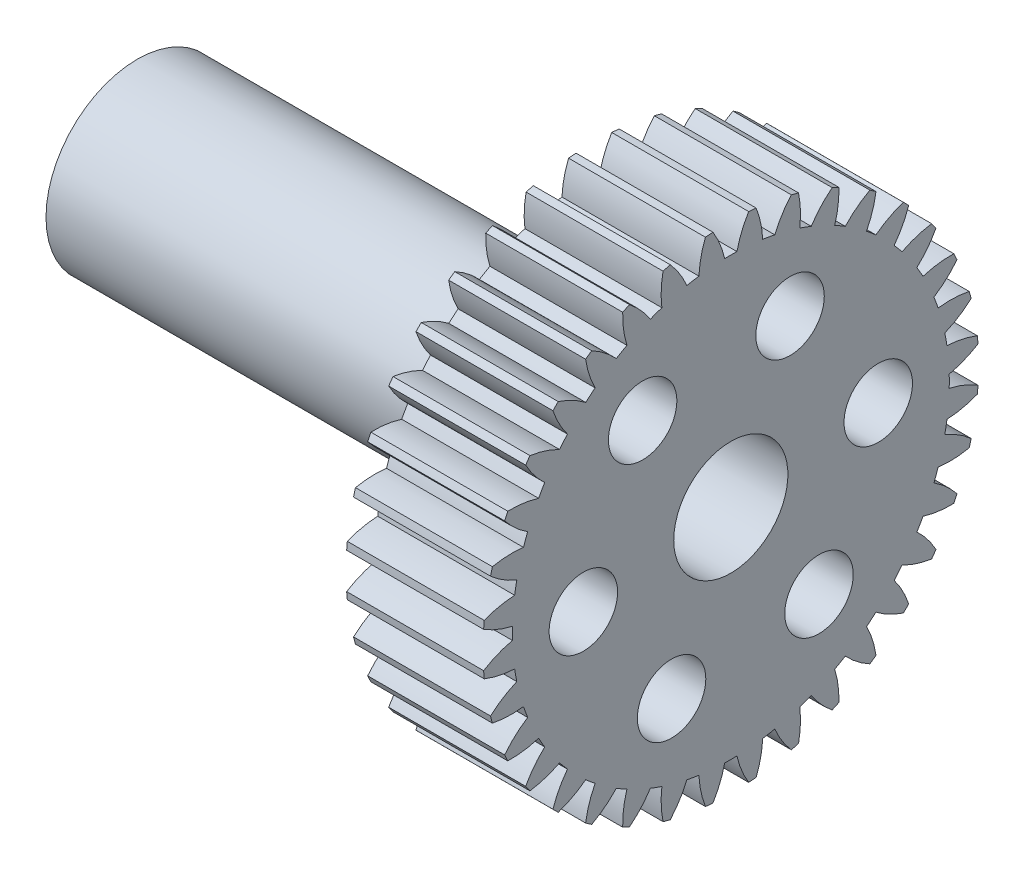
SolidWorks part; units mm, degrees
ref_plane "Plane1" through (0, 0, 0) normal (0, 0, 1) x (1, 0, 0)
ref_plane "Plane2" through (0, 0, 0) normal (0, 1, 0) x (1, 0, 0)
ref_plane "Plane3" through (0, 0, 0) normal (1, 0, 0) x (0, 0, -1)
sketch "HoldingSke" plane through (0, 0, 0) normal (0, 1, 0) x (1, 0, 0)
  line L0 (0, 0) -> (287.6864, -209.0164)
  line L1 (-15, 0) -> (100, 0) construction
  line L2 (0, 0) -> (-2.1039, 2.3779)
  line L3 (0, 0) -> (-11.863, 4.5341)
  line L4 (0, 0) -> (6.9867, 5.0761)
  line L5 (0, 0) -> (-77.3455, -28.8476)
  line L6 (0, 0) -> (-15.7917, -10.6547)
  line L7 (-2.1039, 2.3779) -> (15.665, 82.9929)
  line L8 (-76.2, 54.61) -> (-58.1914, 54.61)
  line L9 (-71.009, 38.7566) -> (-53.1078, 45.2721)
  line L10 (-76.2, 71.12) -> (104.1128, 71.12)
  line L11 (0, 0) -> (-19.05, 0)
  line L12 (-76.2, 101.6) -> (-76.1147, 101.6)
  line L13 (24.9733, 27.94) -> (52.9518, 28.4284)
  line L14 (24.9733, 27.94) -> (24.9746, 27.94)
  line L15 (24.9733, 27.94) -> (100.4006, 29.5858)
  circle A0 centre (0, 0) radius 7.9375
  circle A1 centre (0, 0) radius 12.7
  circle A2 centre (0, 0) radius 12.7
  circle A3 centre (0, 0) radius 7.9375
  dimension "MHD" = 25.4
  dimension "Hub_dia" = 25.4
  dimension "Bore" = 15.875
  dimension "MBD" = 15.875
  dimension "Num_teeth" = 36
  dimension "Pitch" = 355.6
  dimension "Overall_len" = 82.55
  dimension "Show_teeth" = 36
  dimension "Thickness" = 19.05
  dimension "OAL" = 82.5501
  dimension "T_dim" = 18.0086
  dimension "Ap" = 20
  dimension "H" = 19.05
  dimension "Pitch_radius" = 180.3128
  dimension "Width" = 19.05
  dimension "Backlash" = 0.0853
  dimension "Addendum_fac" = 1
  dimension "Dedendum_fac" = 1.25
  dimension "Clearance_fac" = 0.25
  dimension "Dedendum_add" = 0.0013
sketch "BasProSke" plane through (0, 0, 0) normal (0, 1, 0) x (1, 0, 0)
  line L0 (-10, 0) -> (60, 0) construction
  line L1 (0, 0) -> (0, 34.4714)
  line L2 (0, 0) -> (19.05, 0)
  line L3 (19.05, 0) -> (19.05, 34.4714)
  line L4 (19.05, 34.4714) -> (0, 34.4714)
  dimension "Thickness" = 19.05
  dimension "Diameter" = 68.9429
revolve "Base-Revolve" add sketch "BasProSke" angle 360 about L0
sketch "TooCutSke" plane through (0, 0, 0) normal (1, 0, 0) x (0, 0, -1)
  line L1 (0, 0) -> (0, 107) construction
  line L2 (0, 0) -> (-1.5738, 32.6192) construction
  line L3 (0, 0) -> (-5.6882, 65.0161) construction
  line L4 (-1.5738, 32.6192) -> (-2.8441, 32.5081) construction
  arc A0 (0.8517, 30.3761) -> (-0.8517, 30.3761) centre (0, 0) ccw
  arc A1 (2.5015, 34.406) -> (-2.5015, 34.406) centre (0, 0) ccw
  circle A2 centre (0, 0) radius 32.6571 construction
  circle A3 centre (0, 0) radius 30.6877 construction
  arc A4 (-0.8517, 30.3761) -> (-2.5015, 34.406) centre (-13.5966, 27.5112) ccw
  arc A5 (2.5015, 34.406) -> (0.8517, 30.3761) centre (13.5966, 27.5112) ccw
  dimension "Root_dia" = 60.776
  dimension "Overcut_dia" = 68.9937
  dimension "Pitch_dia" = 65.3143
  dimension "Base_dia" = 61.3754
  dimension "Flank_rad" = 13.0629
  dimension "Half_ang" = 5
  dimension "Half_CT" = 1.2751
extrude "ToothCut" cut sketch "TooCutSke" along normal through all
fillet "Breaks" [suppressed] radius 0.0363
fillet "RootFillets" [suppressed] radius 0.4548
pattern_circular "TeethCuts" count 36 over 360 about axis through (0, 0, 0) along (1, 0, 0) of "ToothCut", "RootFillets", "Breaks"
sketch "HubNeaOneSke" plane through (0, 0, 0) normal (-1, 0, 0) x (0, 0, 1)
  circle A0 centre (0, 0) radius 12.7
  dimension "Diameter" = 25.4
extrude "HubNearOne" add sketch "HubNeaOneSke" along normal blind 63.5001
sketch "HubNeaBotSke" plane through (0, 0, 0) normal (-1, 0, 0) x (0, 0, 1)
  circle A0 centre (0, 0) radius 12.7
  dimension "Diameter" = 25.4
extrude "HubNearBoth" [suppressed] add sketch "HubNeaBotSke" along normal blind 31.75
ref_plane "FarPln" through (19.05, 0, 0) normal (1, 0, 0) x (0, 0, -1)
sketch "HubFarSke" plane through (19.05, 0, 0) normal (1, 0, 0) x (0, 0, -1)
  circle A0 centre (0, 0) radius 12.7
  dimension "Diameter" = 25.4
extrude "HubFar" [suppressed] add sketch "HubFarSke" along normal blind 31.75
sketch "BorSke" plane through (0, 0, 0) normal (1, 0, 0) x (0, 0, -1)
  circle A0 centre (0, 0) radius 7.9375
  dimension "Diameter" = 15.875
extrude "Bore" cut sketch "BorSke" along normal mid plane 165.1001
sketch "KeySke" plane through (0, 0, 0) normal (1, 0, 0) x (0, 0, -1)
  line L0 (-2.3813, 0) -> (-2.3813, 10.0711)
  line L1 (-2.3813, 10.0711) -> (2.3813, 10.0711)
  line L2 (2.3813, 10.0711) -> (2.3813, 0)
  line L3 (0, 0) -> (0, 34) construction
  line L4 (-2.3813, 0) -> (2.3813, 0)
  dimension "Offset" = 10.0711
  dimension "Width" = 4.7625
extrude "Keyway" [suppressed] cut sketch "KeySke" along normal mid plane 165.1001
pattern_circular "Keyway2" [suppressed] count 2 every 90 about axis through (-10, 0, 0) along (1, 0, 0)
sketch "Sketch3" plane through (-63.5001, 0, 0) normal (-1, 0, 0) x (0, 0, 1)
  circle A0 centre (0, 0) radius 8.7376
  point P2 (0, 0)
  point P4 (-0.7441, 7.6589)
extrude "Cut-Extrude1" cut sketch "Sketch3" against normal blind 15.875
sketch "Sketch10" plane through (19.05, 0, 0) normal (1, 0, 0) x (0, 0, -1)
  circle A2 centre (-12.2654, 16.5972) radius 4.7625
extrude "Cut-Extrude3" cut sketch "Sketch10" against normal blind 19.05 contours A2
pattern_circular "CirPattern3" count 6 over 360 about axis through (0, 0, 0) along (1, 0, 0) of "Cut-Extrude3"
equation "' \"Pitch@HoldingSke\" = 4"
equation "' \"Num_teeth@HoldingSke\" = 12"
equation "' \"Ap@HoldingSke\" =  20"
equation "' \"Ap@HoldingSke\" = 20"
equation "' \"Width@HoldingSke\" = 0.5"
equation "' \"Hub_dia@HoldingSke\"= 1"
equation "' \"Hub_dia@HoldingSke\" = 1"
equation "' \"Overall_len@HoldingSke\" = 1.0"
equation "' \"Bore@HoldingSke\" = 0.75"
equation "' \"T_dim@HoldingSke\" = 0.85"
equation "' \"Width@KeySke\" = 0.25"
equation "' \"Show_teeth@HoldingSke\" = 13"
equation "' \"Backlash@HoldingSke\" = 0.009"
equation "' \"Addendum_fac@HoldingSke\" = 1.0"
equation "' \"Dedendum_fac@HoldingSke\" = 1.25"
equation "' \"Dedendum_add@HoldingSke\" = 0.00005"
equation "' \"Clearance_fac@HoldingSke\" = 0.25"
equation "' \"Pitch@HoldingSke\" = 0.5"
equation "' \"Num_teeth@HoldingSke\" = 23"
equation "' \"Show_teeth@HoldingSke\" = 23"
equation "' \"Backlash@HoldingSke\" = 0.0375"
equation "\"Overcut_dia@TooCutSke\" = (\"Num_teeth@HoldingSke\" + 2 * \"Addendum_fac@HoldingSke\") / \"Pitch@HoldingSke\" + 0.002"
equation "\"Pitch_dia@TooCutSke\" = \"Num_teeth@HoldingSke\" / \"Pitch@HoldingSke\""
equation "\"Base_dia@TooCutSke\" = \"Num_teeth@HoldingSke\" / \"Pitch@HoldingSke\" * cos((\"Ap@HoldingSke\"  * 3.14159265 / 180))"
equation "\"Root_dia@TooCutSke\" = (\"Num_teeth@HoldingSke\" + 2) / \"Pitch@HoldingSke\" - 2 * (\"Addendum_fac@HoldingSke\" + \"Dedendum_fac@HoldingSke\") / \"Pitch@HoldingSke\" - \"Dedendum_add@HoldingSke\" * 2"
equation "\"Half_ang@TooCutSke\" = 180 / \"Num_teeth@HoldingSke\""
equation "\"Half_CT@TooCutSke\" = \"Num_teeth@HoldingSke\" / \"Pitch@HoldingSke\" * sin((3.14159265 / 2 / \"Num_teeth@HoldingSke\")) / 2 - 7 * \"Backlash@HoldingSke\" / 4"
equation "\"Flank_rad@TooCutSke\" = \"Num_teeth@HoldingSke\" / \"Pitch@HoldingSke\" / 5"
equation "\"Radius@RootFillets\" = \"Clearance_fac@HoldingSke\" / \"Pitch@HoldingSke\" + \"Dedendum_add@HoldingSke\""
equation "\"Break_rad@Breaks\" = 0.02 / \"Pitch@HoldingSke\""
equation "\"Thickness@HoldingSke\" = \"Width@HoldingSke\""
equation "\"OAL@HoldingSke\" = \"Thickness@HoldingSke\""
equation "\"MHD@HoldingSke\" = (\"Num_teeth@HoldingSke\" + 2) / \"Pitch@HoldingSke\" - 2 * (\"Addendum_fac@HoldingSke\" + \"Dedendum_fac@HoldingSke\")  / \"Pitch@HoldingSke\" - \"Dedendum_add@HoldingSke\" * 2"
equation "\"MBD@HoldingSke\" = (\"Num_teeth@HoldingSke\" + 2) / \"Pitch@HoldingSke\" - 2 * (\"Addendum_fac@HoldingSke\" + \"Dedendum_fac@HoldingSke\")  / \"Pitch@HoldingSke\" - \"Dedendum_add@HoldingSke\" * 2 - 0.002"
equation "\"MHD@HoldingSke\" = ((sgn( \"MHD@HoldingSke\" - \"Hub_dia@HoldingSke\" )-1)*( \"MHD@HoldingSke\" - \"Hub_dia@HoldingSke\" ))/-2+ \"Hub_dia@HoldingSke\""
equation "\"MBD@HoldingSke\" = ((sgn( \"MBD@HoldingSke\" - \"Bore@HoldingSke\" )-1)*( \"MBD@HoldingSke\" - \"Bore@HoldingSke\" ))/-2+ \"Bore@HoldingSke\""
equation "\"OAL@HoldingSke\" = ((sgn( \"OAL@HoldingSke\" - \"Overall_len@HoldingSke\" )+1)*( \"OAL@HoldingSke\" - \"Overall_len@HoldingSke\" ))/2 + \"Overall_len@HoldingSke\" + 0.000002"
equation "\"Num_teeth@TeethCuts\" = int( \"Show_teeth@HoldingSke\" ) + 1"
equation "\"Num_teeth@TeethCuts\" = ((sgn( \"Num_teeth@TeethCuts\" - \"Num_teeth@HoldingSke\" )-1)*( \"Num_teeth@TeethCuts\" - \"Num_teeth@HoldingSke\" ))/-2+ \"Num_teeth@HoldingSke\""
equation "\"Num_teeth@TeethCuts\" = ((sgn( \"Num_teeth@TeethCuts\" - 2.0)+1)*( \"Num_teeth@TeethCuts\" - 2.0))/2 +2.0"
equation "\"Angle@TeethCuts\" = 360.0 / \"Num_teeth@HoldingSke\""
equation "\"Diameter@BasProSke\" = (\"Num_teeth@HoldingSke\" + 2 * \"Addendum_fac@HoldingSke\") / \"Pitch@HoldingSke\""
equation "\"Thickness@BasProSke\"  = \"Thickness@HoldingSke\""
equation "' \"Fillet_rad@BasProSke\" =  \"Thickness@HoldingSke\" * 0.05"
equation "' \"Fillet_rad@BasProSke\" = \"Thickness@HoldingSke\" * 0.05"
equation "\"MHD@HoldingSke\" = ((sgn( \"MHD@HoldingSke\" - \"Root_dia@TooCutSke\" )-1)*( \"MHD@HoldingSke\" - \"Root_dia@TooCutSke\" ))/-2+ \"Root_dia@TooCutSke\""
equation "\"Diameter@HubNeaOneSke\" = \"MHD@HoldingSke\""
equation "\"Length@HubNearOne\" = \"OAL@HoldingSke\" - \"Thickness@BasProSke\""
equation "\"Diameter@HubNeaBotSke\" = \"MHD@HoldingSke\""
equation "\"Length@HubNearBoth\" = ( \"OAL@HoldingSke\" - \"Thickness@BasProSke\" ) / 2.0"
equation "\"Thickness@FarPln\" = \"Thickness@BasProSke\""
equation "\"Diameter@HubFarSke\" = \"MHD@HoldingSke\""
equation "\"Length@HubFar\" = ( \"OAL@HoldingSke\" - \"Thickness@BasProSke\" ) / 2.0"
equation "\"Diameter@BorSke\" = \"MBD@HoldingSke\""
equation "\"D1@Bore\" = \"OAL@HoldingSke\" * 2.0"
equation "\"D1@Keyway\" = \"OAL@HoldingSke\" * 2.0"
equation "\"Offset@KeySke\" = \"T_dim@HoldingSke\" - \"MBD@HoldingSke\" / 2.0"
